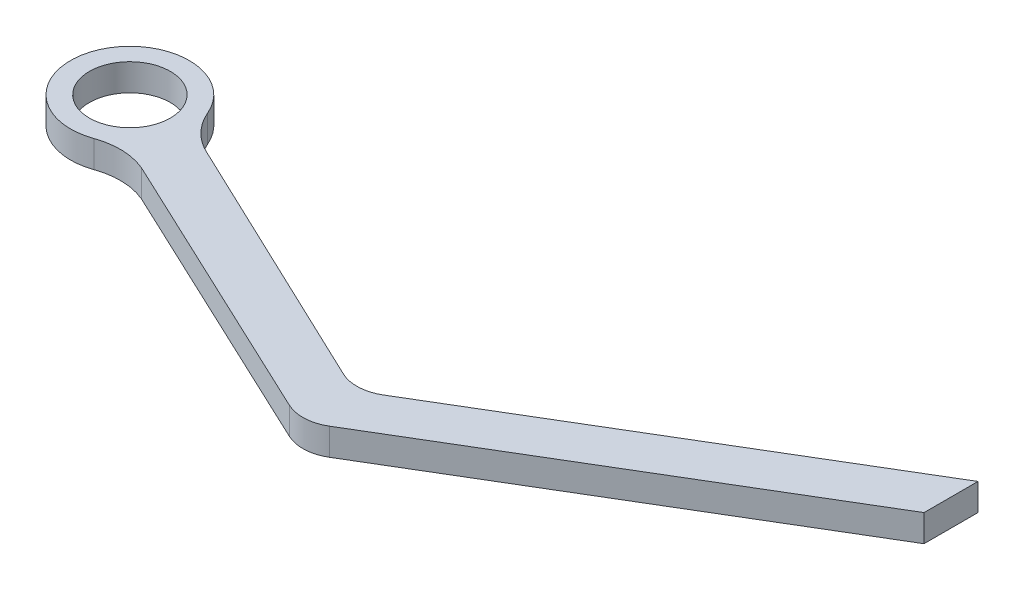
SolidWorks part; units mm, degrees
ref_plane "Front Plane" through (0, 0, 0) normal (0, 0, 1) x (1, 0, 0)
ref_plane "Top Plane" through (0, 0, 0) normal (0, 1, 0) x (1, 0, 0)
ref_plane "Right Plane" through (0, 0, 0) normal (1, 0, 0) x (0, 0, -1)
sketch "Sketch1" plane through (0, 0, 0) normal (0, 1, 0) x (1, 0, 0)
  line L0 (25.8423, -10.0144) -> (6.6937, -0.9196)
  line L1 (25.8459, -14.022) -> (5.1151, -4.2608)
  line L2 (56.2544, 6.6082) -> (28.6685, -9.8796)
  line L9 (28.663, -13.883) -> (56.2544, 2.6082)
  line L10 (56.2544, 2.6082) -> (56.2544, 6.6082)
  arc A0 (4.0463, 1.7237) -> (1.4718, -4.1446) centre (0, 0) ccw
  circle A1 centre (0, 0) radius 3
  arc A2 (25.8423, -10.0144) -> (28.6685, -9.8796) centre (27.1294, -7.3045) ccw
  arc A3 (25.8459, -14.022) -> (28.663, -13.883) centre (27.1239, -11.3079) ccw
  arc A4 (6.6937, -0.9196) -> (4.0463, 1.7237) centre (8.6463, 3.6834) cw
  arc A5 (1.4718, -4.1446) -> (5.1151, -4.2608) centre (3.1449, -8.8563) cw
  dimension "D1" = 3
  dimension "D2" = 3
  dimension "D4" = 5
  dimension "D5" = 5
extrude "Boss-Extrude1" add sketch "Sketch1" along normal blind 2
